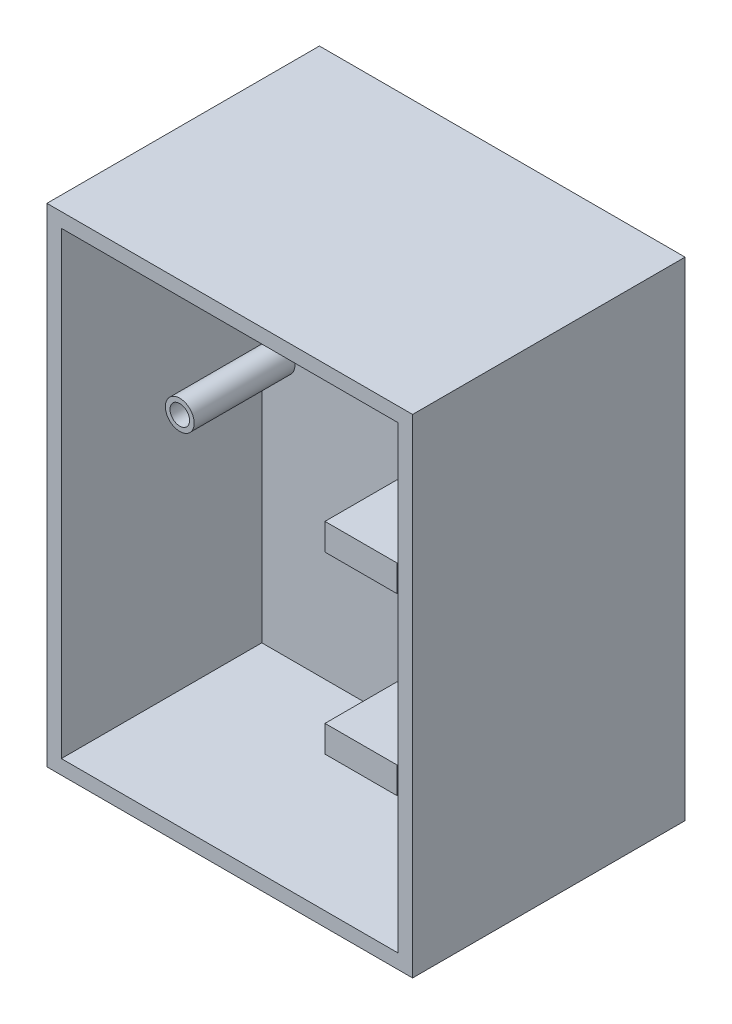
SolidWorks part; units mm, degrees
ref_plane "Front Plane" through (0, 0, 0) normal (0, 0, 1) x (1, 0, 0)
ref_plane "Top Plane" through (0, 0, 0) normal (0, 1, 0) x (1, 0, 0)
ref_plane "Right Plane" through (0, 0, 0) normal (1, 0, 0) x (0, 0, -1)
sketch "Sketch1" plane through (0, 0, 0) normal (0, 0, 1) x (1, 0, 0)
  line L1 (-29.7053, 40.5003) -> (29.7053, 40.5003)
  line L2 (-29.7053, 40.5003) -> (-29.7053, -40.5003)
  line L3 (-29.7053, -40.5003) -> (29.7053, -40.5003)
  line L4 (29.7053, 40.5003) -> (29.7053, -40.5003)
  line L5 (-29.7053, 40.5003) -> (29.7053, -40.5003) construction
  line L6 (-29.7053, -40.5003) -> (29.7053, 40.5003) construction
  point P0 (0, 0)
extrude "Extrude-Thin1" add sketch "Sketch1" along normal blind 35.3568 thin thin type one direction wall 2.54
sketch "Sketch2" plane through (0, 0, 0) normal (0, 0, -1) x (-1, 0, 0)
  line L1 (32.2453, -43.0403) -> (-32.2453, -43.0403)
  line L2 (32.2453, -43.0403) -> (32.2453, 43.0403)
  line L3 (32.2453, 43.0403) -> (-32.2453, 43.0403)
  line L4 (-32.2453, -43.0403) -> (-32.2453, 43.0403)
extrude "Boss-Extrude1" add sketch "Sketch2" along normal blind 12.7
sketch "Sketch3" plane through (0, 0, 0) normal (0, 0, 1) x (1, 0, 0)
  line L0 (-29.7053, -40.5003) -> (-29.7053, -2.4003) construction
  line L1 (-29.7053, 40.5003) -> (-29.7053, -40.5003) construction
  line L2 (-29.7053, -21.4503) -> (29.7053, -21.4503) construction
  line L3 (29.7053, -40.5003) -> (29.7053, 40.5003) construction
  line L4 (6.8363, -13.0617) -> (-5.8637, -13.0617)
  line L5 (-25.781, -34.5313) -> (25.781, -34.5313)
  line L6 (-25.781, -34.5313) -> (-25.781, -8.3693)
  line L7 (-25.781, -8.3693) -> (25.781, -8.3693)
  line L8 (25.781, -34.5313) -> (25.781, -8.3693)
  line L9 (-25.781, -34.5313) -> (25.781, -8.3693) construction
  line L10 (-25.781, -8.3693) -> (25.781, -34.5313) construction
  line L11 (6.8363, -13.0617) -> (6.8363, -3.6769)
  line L12 (-5.8637, -13.0617) -> (-5.8637, -3.6769)
  line L13 (6.8363, -3.6769) -> (-5.8637, -3.6769)
  line L14 (6.8363, -13.0617) -> (-5.8637, -3.6769) construction
  line L15 (-5.8637, -13.0617) -> (6.8363, -3.6769) construction
  line L16 (6.8363, -29.8389) -> (-5.8637, -29.8389)
  line L17 (6.8363, -29.8389) -> (6.8363, -39.2237)
  line L18 (6.8363, -39.2237) -> (-5.8637, -39.2237)
  line L19 (-5.8637, -29.8389) -> (-5.8637, -39.2237)
  point P9 (0, -21.4503)
  point P15 (0.4863, -8.3693)
  dimension "D1" = 12.7
extrude "Boss-Extrude3" add sketch "Sketch3" along normal blind 12.7 contours L11 L13 L12 L7 | L5 L19 L18 L17
sketch "Sketch5" plane through (0, 0, 0) normal (0, 0, 1) x (1, 0, 0)
  line L0 (-29.7053, 0) -> (-29.7053, 40.5003) construction
  line L1 (-29.7053, 40.5003) -> (-29.7053, -40.5003) construction
  line L2 (-29.7053, 40.5003) -> (-29.7053, 20.2502) construction
  line L3 (-29.7053, 20.2502) -> (29.7053, 20.2502) construction
  line L4 (29.7053, -40.5003) -> (29.7053, 40.5003) construction
  line L6 (-26.394, 4.8694) -> (26.394, 4.8694)
  line L7 (-26.394, 4.8694) -> (-26.394, 35.6309)
  line L8 (-26.394, 35.6309) -> (26.394, 35.6309)
  line L9 (26.394, 4.8694) -> (26.394, 35.6309)
  line L10 (-26.394, 4.8694) -> (26.394, 35.6309) construction
  line L11 (-26.394, 35.6309) -> (26.394, 4.8694) construction
  circle A0 centre (-26.394, 35.6309) radius 2.54
  circle A1 centre (-26.394, 4.8694) radius 2.54
  circle A2 centre (26.394, 20.2502) radius 2.54
  circle A3 centre (26.394, 6.3384) radius 2.54
  point P9 (0, 20.2502)
extrude "Boss-Extrude4" add sketch "Sketch5" along normal blind 17.78 contours L7 A1 L6 | L6 A1 L7 | L8 A0 L7 | L9 A2 | L9 A2 | L6 A3 L9 | L9 A3 L6
sketch "Sketch6" plane through (0, 0, 17.78) normal (0, 0, 1) x (1, 0, 0)
  line L0 (-26.394, 2.3294) -> (-26.394, 7.4094) construction
  line L1 (-26.394, 4.8694) -> (-23.854, 4.8694) construction
  circle A0 centre (-26.394, 4.8694) radius 2.54 construction
sketch "Sketch7" plane through (0, 0, 17.78) normal (0, 0, 1) x (1, 0, 0)
  line L0 (-27.0411, 38.087) -> (-25.7468, 33.1747) construction
  line L1 (-26.394, 35.6309) -> (-23.9378, 36.2781) construction
  circle A0 centre (-26.394, 35.6309) radius 2.54 construction
sketch "Sketch8" plane through (0, 0, 17.78) normal (0, 0, 1) x (1, 0, 0)
  line L0 (26.394, 17.7102) -> (26.394, 22.7902) construction
  line L1 (26.394, 20.2502) -> (23.854, 20.2502) construction
  circle A0 centre (26.394, 20.2502) radius 2.54 construction
sketch "Sketch9" plane through (0, 0, 17.78) normal (0, 0, 1) x (1, 0, 0)
  line L0 (26.394, 3.7984) -> (26.394, 8.8784) construction
  line L1 (26.394, 6.3384) -> (23.854, 6.3384) construction
  circle A0 centre (26.394, 6.3384) radius 2.54 construction
hole_wizard "#8-32 Tapped Hole1" positions "3DSketch2" profile "Sketch11" tap size "#8-32" standard "ANSI Inch"
sketch3d "3DSketch2"
  point P0 (-26.394, 4.8694, 17.78)
  point P3 (-26.394, 35.6309, 17.78)
  point P6 (26.394, 20.2502, 17.78)
  point P9 (26.394, 6.3384, 17.78)
sketch "Sketch11" plane through (-26.394, 4.8694, 17.78) normal (1, 0, 0) x (0, -1, 0)
  line L0 (0, 0) -> (0, 19.8338)
  line L1 (0, 19.8338) -> (1.7272, 18.796)
  line L2 (1.7272, 18.796) -> (1.7272, 0)
  line L5 (1.7272, 0) -> (0, 0)
  line L10 (0, 19.8338) -> (-1.7272, 18.796) construction
  line L11 (0, -6.35) -> (0, 107.95) construction
  dimension "Tap Drill Dia." = 3.4544
  dimension "Tap Drill Depth" = 18.796
  dimension "Drill Angle" = 118
cosmetic thread "Hole Thread1" parameters "D1"=16.51, "D2"=4.1656
cosmetic thread "Hole Thread2" parameters "D1"=16.51, "D2"=4.1656
cosmetic thread "Hole Thread3" parameters "D1"=16.51, "D2"=4.1656
cosmetic thread "Hole Thread4" parameters "D1"=16.51, "D2"=4.1656
